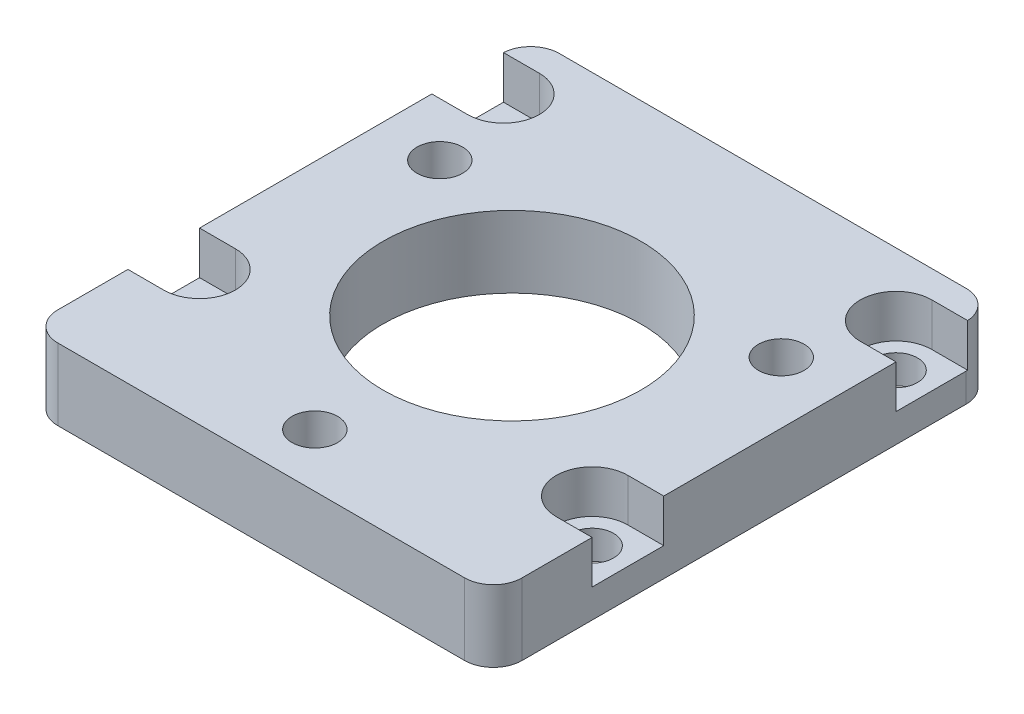
SolidWorks part; units mm, degrees
material "6061 Alloy"
ref_plane "Front" through (0, 0, 0) normal (0, 0, 1) x (1, 0, 0)
ref_plane "Top" through (0, 0, 0) normal (0, 1, 0) x (1, 0, 0)
ref_plane "Right" through (0, 0, 0) normal (1, 0, 0) x (0, 0, -1)
sketch "Sketch1" plane through (0, 0, 0) normal (0, 1, 0) x (1, 0, 0)
  line L1 (20.574, -22.225) -> (-20.574, -22.225)
  line L2 (20.574, -22.225) -> (20.574, 22.225)
  line L3 (20.574, 22.225) -> (-20.574, 22.225)
  line L4 (-20.574, -22.225) -> (-20.574, 22.225)
  line L5 (20.574, -22.225) -> (-20.574, 22.225) construction
  line L6 (20.574, 22.225) -> (-20.574, -22.225) construction
  point P0 (0, 0)
  dimension "D1" = 44.45
  dimension "D2" = 41.148
extrude "Boss-Extrude1" add sketch "Sketch1" along normal blind 6.35
fillet "Fillet1" radius 2.54 4 edges at (-20.574, 3.175, -22.225) (20.574, 3.175, -22.225) (20.574, 3.175, 22.225) (-20.574, 3.175, 22.225)
sketch "Sketch2" plane through (0, 6.35, 0) normal (0, 1, 0) x (1, 0, 0)
  line L0 (0, 0) -> (0, -17.4752) construction
  line L1 (0, 0) -> (-15.134, 8.7376) construction
  line L2 (0, 0) -> (15.134, 8.7376) construction
  circle A0 centre (0, 0) radius 11.43
  point P5 (0, -17.4752)
  point P7 (-15.134, 8.7376)
  point P9 (0, 0)
  point P10 (15.134, 8.7376)
  point P11 (0, 0)
  dimension "D1" = 22.86
  dimension "D3" = 3
  dimension "D2" = 17.4752
extrude "Cut-Extrude1" cut sketch "Sketch2" against normal through all
sketch "Sketch4" plane through (0, 6.35, 0) normal (0, 1, 0) x (1, 0, 0)
  line L0 (-20.574, 19.685) -> (-20.574, -19.685) construction
  line L1 (18.034, 22.225) -> (-18.034, 22.225) construction
  point P0 (-17.399, 16.6454)
  point P1 (-17.399, -10.2954)
  point P2 (17.399, 16.6454)
  point P3 (17.399, -10.2954)
  dimension "D1" = 3.175
  dimension "D2" = 5.5796
  dimension "D3" = 26.9408
  dimension "D4" = 34.798
hole_wizard "#25 (0.1495) Diameter Hole1" positions "3DSketch1" profile "Sketch5" hole size "#25" standard "ANSI Inch" end condition through all
sketch3d "3DSketch1"
  point P0 (-17.399, 6.35, -16.6454)
  point P3 (17.399, 6.35, -16.6454)
  point P6 (17.399, 6.35, 10.2954)
  point P9 (-17.399, 6.35, 10.2954)
sketch "Sketch5" plane through (-17.399, 6.35, -16.6454) normal (1, 0, 0) x (0, 0, 1)
  line L0 (0, 0) -> (0, 6.35)
  line L1 (0, 6.35) -> (1.8986, 6.35)
  line L2 (1.8986, 6.35) -> (1.8986, 0)
  line L5 (1.8986, 0) -> (0, 0)
  line L11 (0, -6.35) -> (0, 107.95) construction
  dimension "Thru Hole Dia." = 3.7973
  dimension "Thru Hole Depth" = 6.35
hole_wizard "#10-32 Tapped Hole2" positions "3DSketch2" profile "Sketch6" tap size "#10-32" standard "ANSI Inch" end condition through all
sketch3d "3DSketch2"
  point P0 (-15.134, 6.35, -8.7376)
  point P3 (15.134, 6.35, -8.7376)
  point P12 (0, 6.35, 17.4752)
sketch "Sketch6" plane through (-15.134, 6.35, -8.7376) normal (1, 0, 0) x (0, 0, 1)
  line L0 (0, 0) -> (0, 6.35)
  line L1 (0, 6.35) -> (2.0193, 6.35)
  line L2 (2.0193, 6.35) -> (2.0193, 0)
  line L5 (2.0193, 0) -> (0, 0)
  line L11 (0, -6.35) -> (0, 107.95) construction
  dimension "Thru Tap Drill Dia." = 4.0386
  dimension "Thru Tap Drill Depth" = 6.35
cosmetic thread "Hole Thread5" parameters "D2"=4.826
cosmetic thread "Hole Thread6" parameters "D2"=4.826
cosmetic thread "Hole Thread7" parameters "D2"=4.826
sketch "Sketch9" plane through (0, 6.35, 0) normal (0, 1, 0) x (1, 0, 0)
  line L0 (-20.574, 13.4704) -> (-20.574, 19.8204)
  line L1 (-20.574, 19.685) -> (-20.574, -19.685) construction
  line L2 (-20.574, 19.8204) -> (-17.399, 19.8204)
  line L3 (-17.399, 13.4704) -> (-20.574, 13.4704)
  line L4 (11.43, 0) -> (0, 0) construction
  line L5 (0, 0) -> (0, 11.43) construction
  line L6 (17.399, 13.4704) -> (20.574, 13.4704)
  line L7 (20.574, 19.8204) -> (17.399, 19.8204)
  line L8 (20.574, 13.4704) -> (20.574, 19.8204)
  line L9 (0, 3.175) -> (10.9802, 3.175) construction
  line L10 (20.574, -7.1204) -> (20.574, -13.4704)
  line L11 (20.574, -13.4704) -> (17.399, -13.4704)
  line L12 (17.399, -7.1204) -> (20.574, -7.1204)
  line L13 (-17.399, -7.1204) -> (-20.574, -7.1204)
  line L14 (-20.574, -13.4704) -> (-17.399, -13.4704)
  line L15 (-20.574, -7.1204) -> (-20.574, -13.4704)
  arc A4 (-17.399, 19.8204) -> (-17.399, 13.4704) centre (-17.399, 16.6454) cw
  circle A5 centre (0, 0) radius 11.43 construction
  arc A6 (17.399, 19.8204) -> (17.399, 13.4704) centre (17.399, 16.6454) ccw
  arc A7 (17.399, -13.4704) -> (17.399, -7.1204) centre (17.399, -10.2954) cw
  arc A8 (-17.399, -13.4704) -> (-17.399, -7.1204) centre (-17.399, -10.2954) ccw
  dimension "D1" = 6.35
  dimension "D2" = 3.175
extrude "Cut-Extrude2" cut sketch "Sketch9" against normal blind 3.81
